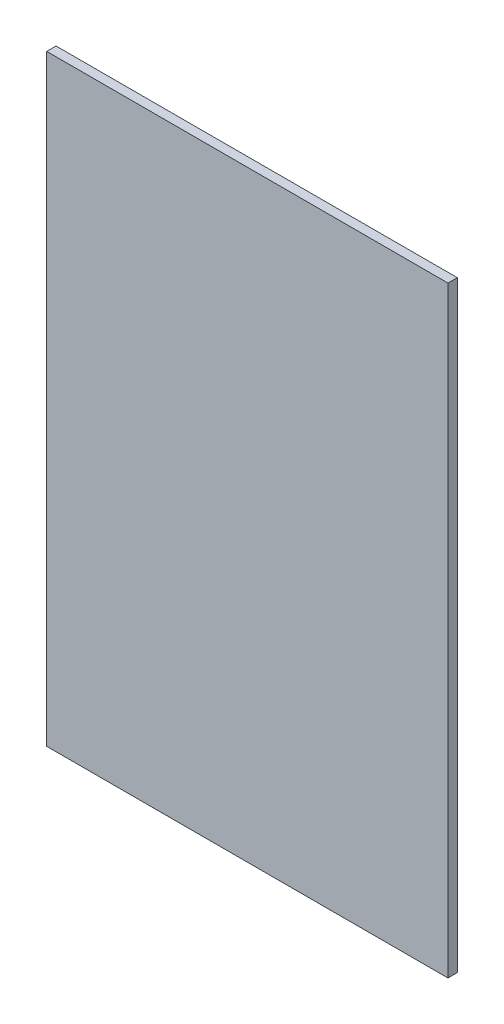
SolidWorks part; units mm, degrees
ref_plane "Front Plane" through (0, 0, 0) normal (0, 0, 1) x (1, 0, 0)
ref_plane "Top Plane" through (0, 0, 0) normal (0, 1, 0) x (1, 0, 0)
ref_plane "Right Plane" through (0, 0, 0) normal (1, 0, 0) x (0, 0, -1)
sketch "Sketch1" plane through (0, 0, 0) normal (0, 0, 1) x (1, 0, 0)
  line L1 (0, 0) -> (101.6, 0)
  line L2 (0, 0) -> (0, 152.4)
  line L3 (0, 152.4) -> (101.6, 152.4)
  line L4 (101.6, 0) -> (101.6, 152.4)
  dimension "D1" = 101.6
  dimension "D2" = 152.4
extrude "Boss-Extrude1" add sketch "Sketch1" along normal blind 2.3622
